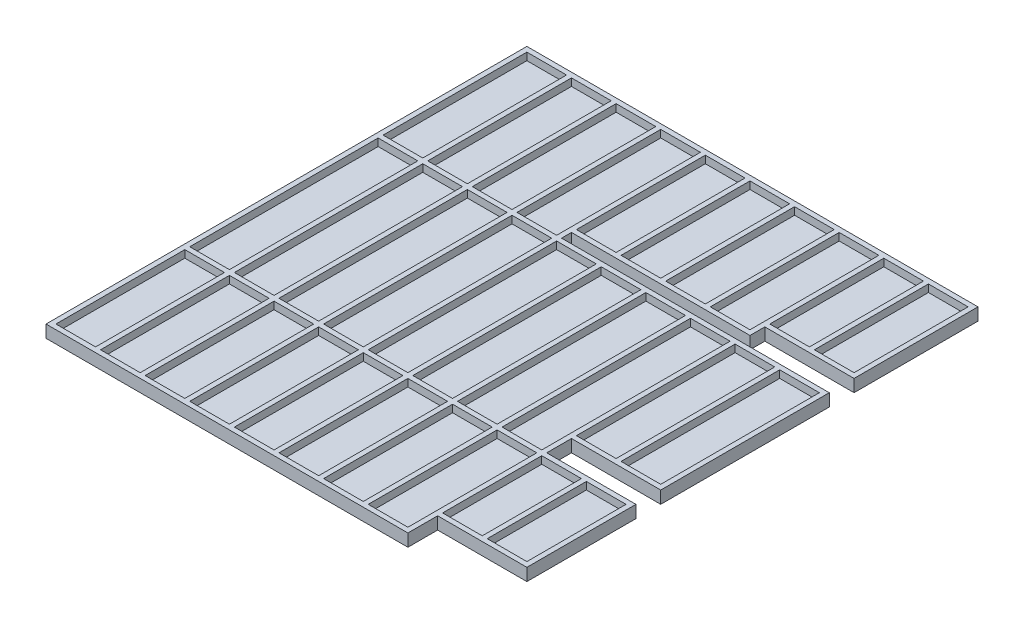
SolidWorks part; units mm, degrees
ref_plane "前视基准面" through (0, 0, 0) normal (0, 0, 1) x (1, 0, 0)
ref_plane "上视基准面" through (0, 0, 0) normal (0, 1, 0) x (1, 0, 0)
ref_plane "右视基准面" through (0, 0, 0) normal (1, 0, 0) x (0, 0, -1)
other "Configuration Table"
sketch "草图2" plane through (0, 0, 0) normal (0, 1, 0) x (1, 0, 0)
  line L0 (0, 0) -> (112.6452, 0) construction
  line L1 (0, 0) -> (8, 0)
  line L2 (0, 0) -> (0, -29)
  line L3 (0, -29) -> (8, -29)
  line L4 (8, 0) -> (8, -29)
  line L5 (0, 0) -> (0, -127.9399) construction
  line L6 (0, -30) -> (108.3236, -30) construction
  line L7 (9, 0) -> (17, 0)
  line L8 (9, 0) -> (9, -29)
  line L9 (9, -29) -> (17, -29)
  line L10 (17, 0) -> (17, -29)
  line L11 (18, 0) -> (26, 0)
  line L12 (18, 0) -> (18, -29)
  line L13 (18, -29) -> (26, -29)
  line L14 (26, 0) -> (26, -29)
  line L15 (27, 0) -> (35, 0)
  line L16 (27, 0) -> (27, -29)
  line L17 (27, -29) -> (35, -29)
  line L18 (35, 0) -> (35, -29)
  line L19 (36, 0) -> (44, 0)
  line L20 (36, 0) -> (36, -26)
  line L21 (36, -26) -> (44, -26)
  line L22 (44, 0) -> (44, -26)
  line L23 (0, -69) -> (108.346, -69) construction
  line L25 (0, -30) -> (8, -30)
  line L26 (0, -30) -> (0, -68)
  line L27 (0, -68) -> (8, -68)
  line L28 (8, -30) -> (8, -68)
  line L29 (0, -69) -> (8, -69)
  line L30 (0, -69) -> (0, -95)
  line L31 (0, -95) -> (8, -95)
  line L32 (8, -69) -> (8, -95)
  line L33 (45, 0) -> (53, 0)
  line L34 (45, 0) -> (45, -26)
  line L35 (45, -26) -> (53, -26)
  line L36 (53, 0) -> (53, -26)
  line L37 (54, 0) -> (62, 0)
  line L38 (54, 0) -> (54, -26)
  line L39 (54, -26) -> (62, -26)
  line L40 (62, 0) -> (62, -26)
  line L41 (63, 0) -> (71, 0)
  line L42 (63, 0) -> (63, -26)
  line L43 (63, -26) -> (71, -26)
  line L44 (71, 0) -> (71, -26)
  line L45 (72, 0) -> (80, 0)
  line L46 (72, 0) -> (72, -23)
  line L47 (72, -23) -> (80, -23)
  line L48 (80, 0) -> (80, -23)
  line L49 (81, 0) -> (89, 0)
  line L50 (81, 0) -> (81, -23)
  line L51 (81, -23) -> (89, -23)
  line L52 (89, 0) -> (89, -23)
  line L53 (9, -30) -> (17, -30)
  line L54 (9, -30) -> (9, -68)
  line L55 (9, -68) -> (17, -68)
  line L56 (17, -30) -> (17, -68)
  line L57 (18, -30) -> (26, -30)
  line L58 (18, -30) -> (18, -68)
  line L59 (18, -68) -> (26, -68)
  line L60 (26, -30) -> (26, -68)
  line L61 (27, -30) -> (35, -30)
  line L62 (27, -30) -> (27, -68)
  line L63 (27, -68) -> (35, -68)
  line L64 (35, -30) -> (35, -68)
  line L65 (36, -30) -> (44, -30)
  line L66 (36, -30) -> (36, -68)
  line L67 (36, -68) -> (44, -68)
  line L68 (44, -30) -> (44, -68)
  line L69 (45, -30) -> (53, -30)
  line L70 (45, -30) -> (45, -68)
  line L71 (45, -68) -> (53, -68)
  line L72 (53, -30) -> (53, -68)
  line L73 (54, -30) -> (62, -30)
  line L74 (54, -30) -> (54, -68)
  line L75 (54, -68) -> (62, -68)
  line L76 (62, -30) -> (62, -68)
  line L77 (63, -30) -> (71, -30)
  line L78 (63, -30) -> (63, -68)
  line L79 (63, -68) -> (71, -68)
  line L80 (71, -30) -> (71, -68)
  line L81 (72, -30) -> (80, -30)
  line L82 (72, -30) -> (72, -62)
  line L83 (72, -62) -> (80, -62)
  line L84 (80, -30) -> (80, -62)
  line L85 (81, -30) -> (89, -30)
  line L86 (81, -30) -> (81, -62)
  line L87 (81, -62) -> (89, -62)
  line L88 (89, -30) -> (89, -62)
  line L89 (9, -69) -> (17, -69)
  line L90 (9, -69) -> (9, -95)
  line L91 (9, -95) -> (17, -95)
  line L92 (17, -69) -> (17, -95)
  line L93 (18, -69) -> (26, -69)
  line L94 (18, -69) -> (18, -95)
  line L95 (18, -95) -> (26, -95)
  line L96 (26, -69) -> (26, -95)
  line L97 (27, -69) -> (35, -69)
  line L98 (27, -69) -> (27, -95)
  line L99 (27, -95) -> (35, -95)
  line L100 (35, -69) -> (35, -95)
  line L101 (36, -69) -> (44, -69)
  line L102 (36, -69) -> (36, -95)
  line L103 (36, -95) -> (44, -95)
  line L104 (44, -69) -> (44, -95)
  line L105 (45, -69) -> (53, -69)
  line L106 (45, -69) -> (45, -95)
  line L107 (45, -95) -> (53, -95)
  line L108 (53, -69) -> (53, -95)
  line L109 (54, -69) -> (62, -69)
  line L110 (54, -69) -> (54, -95)
  line L111 (54, -95) -> (62, -95)
  line L112 (62, -69) -> (62, -95)
  line L117 (63, -69) -> (71, -69)
  line L118 (63, -69) -> (63, -95)
  line L119 (63, -95) -> (71, -95)
  line L120 (71, -69) -> (71, -95)
  line L121 (72, -69) -> (80, -69)
  line L122 (72, -69) -> (72, -89)
  line L123 (72, -89) -> (80, -89)
  line L124 (80, -69) -> (80, -89)
  line L125 (81, -69) -> (89, -69)
  line L126 (81, -69) -> (81, -89)
  line L127 (81, -89) -> (89, -89)
  line L128 (89, -69) -> (89, -89)
  dimension "D1" = 8
  dimension "D2" = 8
  dimension "D3" = 8
  dimension "D4" = 8
  dimension "D5" = 8
  dimension "1" = 1
  dimension "D6" = 1
  dimension "D7" = 1
  dimension "D8" = 1
  dimension "D9" = 29
  dimension "D10" = 29
  dimension "D11" = 29
  dimension "D12" = 29
  dimension "D13" = 26
  dimension "D14" = 26
  dimension "D15" = 26
  dimension "D16" = 26
  dimension "D17" = 23
  dimension "D18" = 23
  dimension "D19" = 8
  dimension "D20" = 8
  dimension "D21" = 8
  dimension "D22" = 8
  dimension "D23" = 8
  dimension "D24" = 1
  dimension "D25" = 1
  dimension "D26" = 1
  dimension "D27" = 1
  dimension "D28" = 1
  dimension "D29" = 8
  dimension "D30" = 30
  dimension "D31" = 38
  dimension "D32" = 38
  dimension "D33" = 38
  dimension "D34" = 38
  dimension "D35" = 38
  dimension "D36" = 38
  dimension "D37" = 38
  dimension "D38" = 38
  dimension "D39" = 32
  dimension "D40" = 32
  dimension "D41" = 39
  dimension "D42" = 26
  dimension "D43" = 20
  dimension "D44" = 20
  dimension "D45" = 26
  dimension "D46" = 26
  dimension "D47" = 26
  dimension "D48" = 26
  dimension "D49" = 26
  dimension "D50" = 26
  dimension "D51" = 26
sketch "草图3" plane through (0, 0, 0) normal (0, 1, 0) x (1, 0, 0)
  line L0 (0, 0) -> (8, 0) construction
  line L1 (-1, 1) -> (90, 1)
  line L2 (-1, 1) -> (-1, -96)
  line L3 (-1, -96) -> (90, -96)
  line L4 (90, 1) -> (90, -96)
  line L5 (0, 0) -> (0, -29) construction
  line L6 (89, 0) -> (89, -23) construction
  line L7 (0, -95) -> (8, -95) construction
  line L8 (81, -89) -> (89, -89) construction
  line L9 (90, -96) -> (72, -96)
  line L10 (90, -96) -> (90, -90)
  line L11 (90, -90) -> (72, -90)
  line L12 (72, -96) -> (72, -90)
  line L13 (90, -68) -> (72, -68)
  line L14 (90, -68) -> (90, -63)
  line L15 (90, -63) -> (72, -63)
  line L16 (72, -68) -> (72, -63)
  line L17 (90, -24) -> (72, -24)
  line L18 (90, -24) -> (90, -29)
  line L19 (90, -29) -> (72, -29)
  line L20 (72, -24) -> (72, -29)
  line L21 (71, -69) -> (71, -95) construction
  line L22 (81, -62) -> (89, -62) construction
  line L23 (81, -69) -> (89, -69) construction
  line L24 (71, -30) -> (71, -68) construction
  line L25 (71, 0) -> (71, -26) construction
  line L26 (81, -23) -> (89, -23) construction
  line L27 (81, -30) -> (89, -30) construction
  line L28 (54, -26) -> (62, -26) construction
  line L29 (72, -29) -> (36, -29)
  line L30 (72, -29) -> (72, -27)
  line L31 (72, -27) -> (36, -27)
  line L32 (36, -29) -> (36, -27)
  line L33 (35, 0) -> (35, -29) construction
  dimension "D1" = 1
  dimension "D2" = 1
  dimension "D3" = 1
  dimension "D4" = 1
  dimension "D5" = 1
  dimension "D6" = 1
  dimension "D7" = 1
  dimension "D8" = 1
  dimension "D9" = 1
  dimension "D10" = 1
  dimension "D11" = 1
  dimension "D12" = 1
  dimension "D13" = 1
  dimension "D14" = 1
extrude "凸台-拉伸2" add sketch "草图3" along normal blind 2.5 contours L20 L17 L4 L1 L2 L3 L12 L11 L13 L16 L15 L19
extrude "切除-拉伸2" cut sketch "草图2" along normal blind 1.5 from offset 1
equation "\"w\"= 8"
equation "\"D1@草图2\"=\"w\""
equation "\"D2@草图2\"=\"w\""
equation "\"D3@草图2\"=\"w\""
equation "\"D4@草图2\"=\"w\""
equation "\"D5@草图2\"=\"w\""
equation "\"D19@草图2\"=\"w\""
equation "\"D20@草图2\"=\"w\""
equation "\"D21@草图2\"=\"w\""
equation "\"D22@草图2\"=\"w\""
equation "\"D23@草图2\"=\"w\""
equation "\"D29@草图2\"=\"w\""
